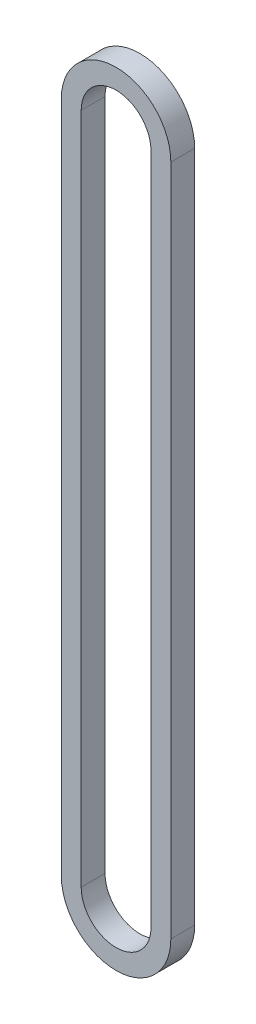
SolidWorks part; units mm, degrees
ref_plane "Front Plane" through (0, 0, 0) normal (0, 0, 1) x (1, 0, 0)
ref_plane "Top Plane" through (0, 0, 0) normal (0, 1, 0) x (1, 0, 0)
ref_plane "Right Plane" through (0, 0, 0) normal (1, 0, 0) x (0, 0, -1)
sketch "Sketch1" plane through (0, 0, 0) normal (0, 0, 1) x (1, 0, 0)
  line L0 (0, 0) -> (0, 215) construction
  line L1 (-11.1506, 0) -> (-11.1506, 215)
  line L2 (11.1506, 0) -> (11.1506, 215)
  line L3 (-17.5006, 0) -> (-17.5006, 215)
  line L4 (17.5006, 0) -> (17.5006, 215)
  arc A0 (-11.1506, 0) -> (11.1506, 0) centre (0, 0) ccw
  arc A1 (11.1506, 215) -> (-11.1506, 215) centre (0, 215) ccw
  arc A2 (17.5006, 215) -> (-17.5006, 215) centre (0, 215) ccw
  arc A3 (-17.5006, 0) -> (17.5006, 0) centre (0, 0) ccw
  point P3 (0, 107.5)
  dimension "D2" = 11.1506
  dimension "D1" = 215
  dimension "D3" = 6.35
extrude "Boss-Extrude1" add sketch "Sketch1" along normal blind 7.62
